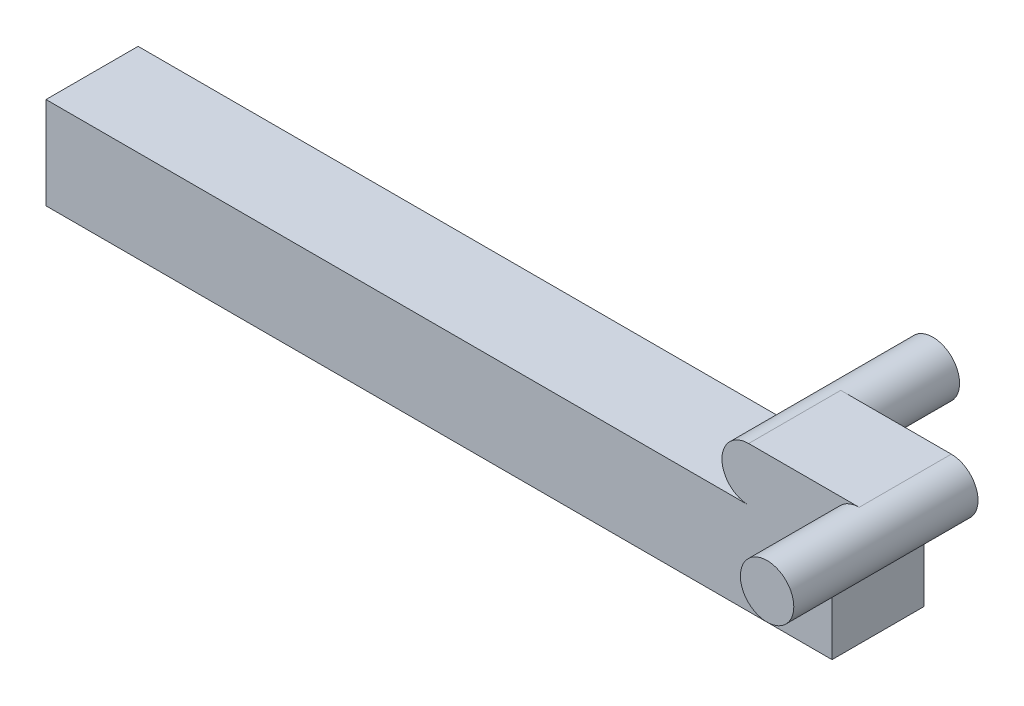
SolidWorks part; units mm, degrees
ref_plane "前视基准面" through (0, 0, 0) normal (0, 0, 1) x (1, 0, 0)
ref_plane "上视基准面" through (0, 0, 0) normal (0, 1, 0) x (1, 0, 0)
ref_plane "右视基准面" through (0, 0, 0) normal (1, 0, 0) x (0, 0, -1)
sketch "草图1" plane through (0, 0, 0) normal (0, 0, 1) x (1, 0, 0)
  line L0 (0, 0) -> (6, 0) construction
  line L1 (0, 1.45) -> (6, 1.45)
  line L2 (0, -1.45) -> (6, -1.45)
  arc A0 (0, 1.45) -> (0, -1.45) centre (0, 0) ccw
  arc A1 (6, -1.45) -> (6, 1.45) centre (6, 0) ccw
  point P3 (3, 0)
extrude "凸台-拉伸1" add sketch "草图1" along normal blind 5
sketch "草图2" plane through (0, 0, 5) normal (0, 0, 1) x (1, 0, 0)
  circle A0 centre (6, 0) radius 1.45
extrude "凸台-拉伸2" add sketch "草图2" along normal blind 5
sketch "草图3" plane through (0, 0, 0) normal (0, 0, -1) x (-1, 0, 0)
  circle A0 centre (0, 0) radius 1.45
extrude "凸台-拉伸3" add sketch "草图3" along normal blind 5
sketch "草图4" plane through (0, -1.45, 0) normal (0, -1, 0) x (1, 0, 0)
  line L0 (0, 5) -> (6, 5) construction
  line L1 (1.8555, 5) -> (4.5259, 5)
  line L2 (1.8555, 5) -> (1.8555, 0)
  line L3 (1.8555, 0) -> (4.5259, 0)
  line L4 (4.5259, 5) -> (4.5259, 0)
  line L5 (0, 0) -> (6, 0) construction
extrude "凸台-拉伸4" add sketch "草图4" along normal blind 5
sketch "草图5" plane through (1.8555, 0, 0) normal (-1, 0, 0) x (0, 0, 1)
  line L1 (5, -1.45) -> (0, -1.45)
  line L2 (5, -1.45) -> (5, -6.45)
  line L3 (5, -6.45) -> (0, -6.45)
  line L4 (0, -1.45) -> (0, -6.45)
extrude "凸台-拉伸5" add sketch "草图5" along normal blind 40
